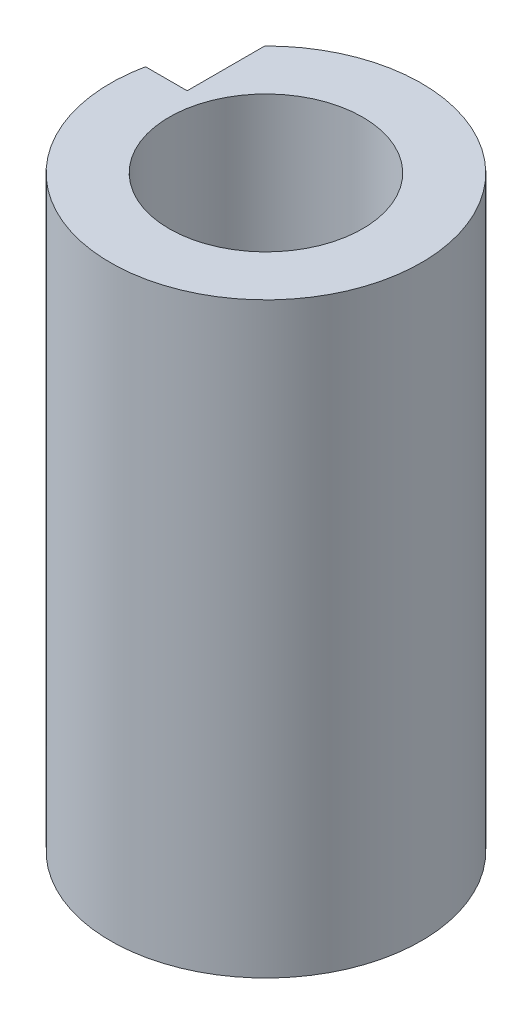
SolidWorks part; units mm, degrees
ref_plane "Front Plane" through (0, 0, 0) normal (0, 0, 1) x (1, 0, 0)
ref_plane "Top Plane" through (0, 0, 0) normal (0, 1, 0) x (1, 0, 0)
ref_plane "Right Plane" through (0, 0, 0) normal (1, 0, 0) x (0, 0, -1)
sketch "Sketch1" plane through (0, -3.714, 0) normal (0, 1, 0) x (1, 0, 0)
  line L0 (-118.4992, 12.3128) -> (-118.4992, 11.1909)
  line L1 (-118.4992, 11.1909) -> (-119.1017, 11.1909)
  line L2 (-118.8992, 11.5909) -> (-130.8992, 11.5909) construction
  line L3 (-118.8992, 11.5909) -> (-118.8992, 20.5909) construction
  circle A0 centre (-116.8992, 10.7309) radius 2.25
  circle A1 centre (-116.8992, 10.7309) radius 2.25 construction
  circle A3 centre (-116.8992, 10.7309) radius 1.4
  circle A4 centre (-116.8992, 10.7309) radius 1.4 construction
  dimension "D1" = 0.4
  dimension "D2" = 0.4
extrude "Boss-Extrude1" add sketch "Sketch1" along normal offset from surface (8.5 mm away) 2.5 contours L1 A0 L0
